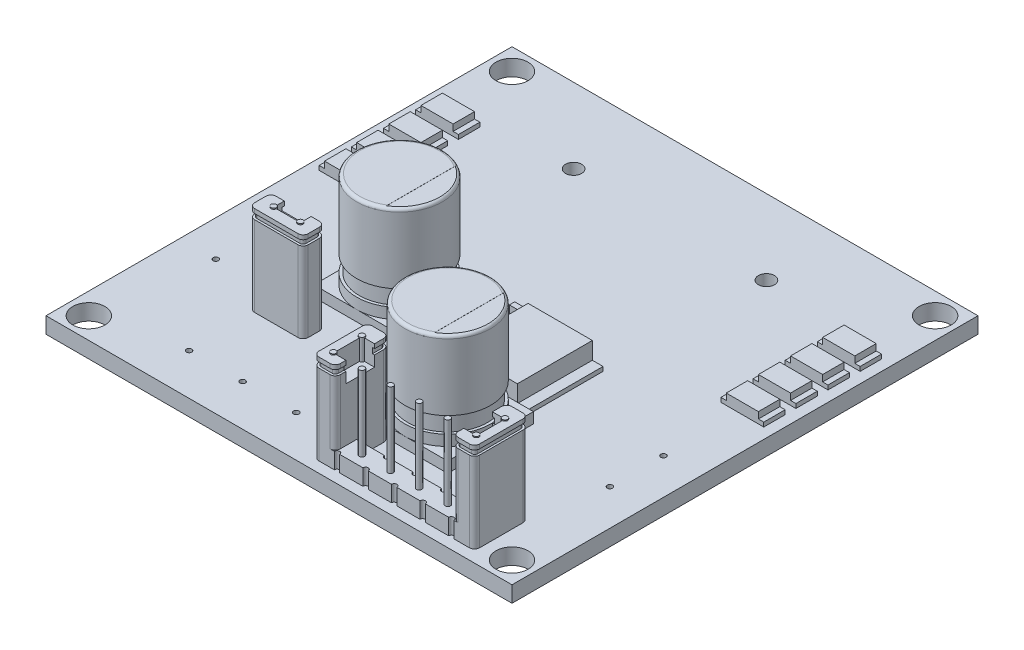
SolidWorks part; units mm, degrees
ref_plane "Ön Düzlem" through (0, 0, 0) normal (0, 0, 1) x (1, 0, 0)
ref_plane "Üst Düzlem" through (0, 0, 0) normal (0, 1, 0) x (1, 0, 0)
ref_plane "Sağ Düzlem" through (0, 0, 0) normal (1, 0, 0) x (0, 0, -1)
sketch "Çizim1" plane through (0, 0, 0) normal (0, 1, 0) x (1, 0, 0)
  line L0 (0, 0) -> (0, 21.75) construction
  line L1 (-21.75, 21.75) -> (21.75, 21.75)
  line L2 (-21.75, 21.75) -> (-21.75, -21.75)
  line L3 (-21.75, -21.75) -> (21.75, -21.75)
  line L4 (21.75, 21.75) -> (21.75, -21.75)
  line L5 (-21.75, 21.75) -> (21.75, -21.75) construction
  line L6 (-21.75, -21.75) -> (21.75, 21.75) construction
  line L7 (0, 21.75) -> (0, 0) construction
  line L8 (0, 0) -> (21.75, 0) construction
  circle A0 centre (-19.75, 19.75) radius 1.5
  circle A1 centre (19.75, 19.75) radius 1.5
  circle A2 centre (19.75, -19.75) radius 1.5
  circle A3 centre (-19.75, -19.75) radius 1.5
  point P0 (0, 0)
  dimension "D3" = 3
  dimension "D5" = 2
  dimension "D1" = 43.5
  dimension "D2" = 43.5
  dimension "D4" = 2
extrude "Yükseklik-Ekstrüzyon1" add sketch "Çizim1" along normal blind 1.5
sketch "Çizim2" plane through (0, 1.5, 0) normal (0, 1, 0) x (1, 0, 0)
  line L0 (0, 21.75) -> (0, 0) construction
  line L1 (21.75, 21.75) -> (-21.75, 21.75) construction
  line L2 (-21.75, 14.75) -> (21.75, 14.75) construction
  line L3 (-21.75, 21.75) -> (-21.75, -21.75) construction
  line L4 (21.75, -21.75) -> (21.75, 21.75) construction
  circle A0 centre (-9, 14.75) radius 0.75
  circle A1 centre (9, 14.75) radius 0.75
  dimension "D2" = 9
  dimension "D3" = 1.5
  dimension "D1" = 9
  dimension "D4" = 7
extrude "Kes-Ekstrüzyon1" cut sketch "Çizim2" against normal blind 10
sketch "Çizim3" plane through (0, 1.5, 0) normal (0, 1, 0) x (1, 0, 0)
  line L0 (-21.75, -3.75) -> (21.75, -3.75) construction
  line L1 (-21.75, 21.75) -> (-21.75, -21.75) construction
  line L2 (21.75, -21.75) -> (21.75, 21.75) construction
  line L3 (-21.75, -21.75) -> (21.75, -21.75) construction
  line L4 (-6.75, 21.75) -> (-6.75, -21.75) construction
  line L5 (21.75, 21.75) -> (-21.75, 21.75) construction
  line L6 (5.75, 21.75) -> (5.75, -21.75) construction
  line L7 (-10.75, 0.25) -> (-2.75, 0.25)
  line L8 (-10.75, 0.25) -> (-10.75, -7.75)
  line L9 (-10.75, -7.75) -> (-2.75, -7.75)
  line L10 (-2.75, 0.25) -> (-2.75, -7.75)
  line L11 (-10.75, 0.25) -> (-2.75, -7.75) construction
  line L12 (-10.75, -7.75) -> (-2.75, 0.25) construction
  line L13 (-21.75, -11.75) -> (21.75, -11.75) construction
  line L15 (1.75, -7.75) -> (9.75, -7.75)
  line L16 (1.75, -7.75) -> (1.75, -15.75)
  line L17 (1.75, -15.75) -> (9.75, -15.75)
  line L18 (9.75, -7.75) -> (9.75, -15.75)
  line L19 (1.75, -7.75) -> (9.75, -15.75) construction
  line L20 (1.75, -15.75) -> (9.75, -7.75) construction
  point P12 (-6.75, -3.75)
  point P21 (5.75, -11.75)
  dimension "D1" = 18
  dimension "D2" = 15
  dimension "D3" = 8
  dimension "D4" = 8
  dimension "D5" = 16
  dimension "D6" = 10
  dimension "D7" = 8
  dimension "D8" = 8
extrude "Yükseklik-Ekstrüzyon2" add sketch "Çizim3" along normal blind 1
sketch "Çizim4" plane through (0, 2.5, 0) normal (0, 1, 0) x (1, 0, 0)
  line L0 (-10.75, 0.25) -> (-2.75, -7.75) construction
  line L1 (1.75, -7.75) -> (9.75, -15.75) construction
  circle A0 centre (-6.75, -3.75) radius 4
  circle A1 centre (5.75, -11.75) radius 4
extrude "Yükseklik-Ekstrüzyon3" add sketch "Çizim4" along normal blind 1
sketch "Çizim5" plane through (0, 3.5, 0) normal (0, 1, 0) x (1, 0, 0)
  circle A0 centre (-6.75, -3.75) radius 3.75
  circle A1 centre (5.75, -11.75) radius 3.75
  dimension "D1" = 7.5
  dimension "D2" = 7.5
extrude "Yükseklik-Ekstrüzyon4" add sketch "Çizim5" along normal blind 1.5
sketch "Çizim6" plane through (0, 5, 0) normal (0, 1, 0) x (1, 0, 0)
  circle A0 centre (-6.75, -3.75) radius 4
  circle A1 centre (5.75, -11.75) radius 4
extrude "Yükseklik-Ekstrüzyon5" add sketch "Çizim6" along normal blind 6.5
fillet "Radyus1" radius 0.3 2 edges at (5.75, 11.5, 15.75) (-6.75, 11.5, 7.75)
sketch "Çizim7" plane through (0, 11.5, 0) normal (0, 1, 0) x (1, 0, 0)
  line L0 (-6.75, -3.75) -> (-6.75, 0.25) construction
  line L1 (-4.7498, -0.286) -> (-4.7498, -7.214)
  line L2 (5.75, -11.75) -> (5.75, -7.75) construction
  line L3 (7.75, -8.2859) -> (7.75, -15.2141)
  arc A0 (-4.7498, -7.214) -> (-4.7498, -0.286) centre (-6.75, -3.75) ccw
  arc A1 (7.75, -15.2141) -> (7.75, -8.2859) centre (5.75, -11.75) ccw
  dimension "D1" = 2.0002
  dimension "D2" = 2
extrude "Kes-Ekstrüzyon2" cut sketch "Çizim7" against normal blind 0.01
sketch "Çizim8" plane through (0, 1.5, 0) normal (0, 1, 0) x (1, 0, 0)
  line L0 (21.75, -20.75) -> (15.3333, -20.75) construction
  line L1 (21.75, -21.75) -> (21.75, 21.75) construction
  line L2 (-21.75, 21.75) -> (-21.75, -21.75) construction
  line L3 (-21.75, -21.75) -> (21.75, -21.75) construction
  line L4 (17.25, -21.75) -> (17.25, 21.75) construction
  line L5 (21.75, 21.75) -> (-21.75, 21.75) construction
  line L6 (4.25, -18.75) -> (6.8333, -18.75)
  line L7 (16.7735, -20.75) -> (15.3333, -20.75)
  line L8 (17.25, -20.2735) -> (17.25, -16.2265)
  line L9 (16.7735, -15.75) -> (15.7265, -15.75)
  line L10 (2.25, -20.2735) -> (2.25, -16.2265)
  line L11 (4.25, -16.2265) -> (4.25, -18.75)
  line L12 (15.25, -16.2265) -> (15.25, -18.75)
  line L13 (3.7735, -15.75) -> (2.7265, -15.75)
  line L15 (6.8333, -20.75) -> (4.6667, -20.75)
  line L16 (6.8333, -20.75) -> (4.6667, -20.75) construction
  line L17 (2.25, -19.75) -> (17.25, -19.75) construction
  line L18 (16.425, -19.75) -> (16.425, -15.75) construction
  line L19 (10, -18.75) -> (12.1667, -18.75)
  line L20 (9.5, -20.75) -> (7.3333, -20.75)
  line L21 (9.5, -20.75) -> (7.3333, -20.75) construction
  line L22 (12.6667, -18.75) -> (15.25, -18.75)
  line L23 (12.1667, -20.75) -> (10, -20.75) construction
  line L24 (12.1667, -20.75) -> (10, -20.75)
  line L25 (14.8333, -20.75) -> (12.6667, -20.75) construction
  line L26 (14.8333, -20.75) -> (12.6667, -20.75)
  line L27 (4.1667, -20.75) -> (2.7265, -20.75)
  line L28 (4.1667, -20.75) -> (-21.75, -20.75) construction
  line L29 (7.3333, -18.75) -> (9.5, -18.75)
  circle A0 centre (19.75, -19.75) radius 1.5 construction
  arc A1 (15.25, -16.2265) -> (15.7265, -15.75) centre (15.7265, -16.2265) cw
  arc A2 (17.25, -16.2265) -> (16.7735, -15.75) centre (16.7735, -16.2265) ccw
  arc A3 (16.7735, -20.75) -> (17.25, -20.2735) centre (16.7735, -20.2735) ccw
  arc A4 (2.7265, -20.75) -> (2.25, -20.2735) centre (2.7265, -20.2735) cw
  arc A5 (4.25, -16.2265) -> (3.7735, -15.75) centre (3.7735, -16.2265) ccw
  arc A6 (2.7265, -15.75) -> (2.25, -16.2265) centre (2.7265, -16.2265) ccw
  circle A7 centre (11.085, -19.75) radius 0.25
  circle A8 centre (13.755, -19.75) radius 0.25
  circle A9 centre (16.425, -19.75) radius 0.25
  circle A10 centre (16.425, -17.08) radius 0.25
  arc A11 (9.5, -18.75) -> (10, -18.75) centre (9.75, -18.75) ccw
  arc A12 (12.1667, -18.75) -> (12.6667, -18.75) centre (12.4167, -18.75) ccw
  arc A13 (10, -20.75) -> (9.5, -20.75) centre (9.75, -20.75) ccw
  arc A14 (12.6667, -20.75) -> (12.1667, -20.75) centre (12.4167, -20.75) ccw
  arc A15 (15.3333, -20.75) -> (14.8333, -20.75) centre (15.0833, -20.75) ccw
  circle A16 centre (3.075, -17.08) radius 0.25
  circle A17 centre (3.075, -19.75) radius 0.25
  arc A18 (4.1667, -20.75) -> (4.6667, -20.75) centre (4.4167, -20.75) cw
  circle A19 centre (5.745, -19.75) radius 0.25
  arc A20 (6.8333, -20.75) -> (7.3333, -20.75) centre (7.0833, -20.75) cw
  arc A21 (7.3333, -18.75) -> (6.8333, -18.75) centre (7.0833, -18.75) cw
  circle A22 centre (8.415, -19.75) radius 0.25
  point P26 (17.25, -15.75)
  point P29 (17.25, -20.75)
  point P32 (2.25, -20.75)
  point P35 (4.25, -15.75)
  dimension "D2" = 2.5
  dimension "D8" = 0.4765
  dimension "D13" = 0.5
  dimension "D14" = 2.67
  dimension "D15" = 2.67
  dimension "D16" = 2.67
  dimension "D17" = 0.5
  dimension "D18" = 0.5
  dimension "D1" = 1
  dimension "D3" = 5
  dimension "D4" = 2
  dimension "D5" = 15
  dimension "D6" = 2
  dimension "D7" = 2
  dimension "D11" = 1
extrude "Yükseklik-Ekstrüzyon6" add sketch "Çizim8" along normal blind 1.5
sketch "Çizim9" plane through (0, 3, 0) normal (0, 1, 0) x (1, 0, 0)
  circle A0 centre (3.075, -17.08) radius 0.25
  circle A1 centre (3.075, -19.75) radius 0.25
  circle A2 centre (5.745, -19.75) radius 0.25
  circle A3 centre (8.415, -19.75) radius 0.25
  circle A4 centre (11.085, -19.75) radius 0.25
  circle A5 centre (13.755, -19.75) radius 0.25
  circle A6 centre (16.425, -19.75) radius 0.25
  circle A7 centre (16.425, -17.08) radius 0.25
extrude "Kes-Ekstrüzyon3" cut sketch "Çizim9" against normal blind 5
sketch "Çizim10" plane through (0, 3, 0) normal (0, 1, 0) x (1, 0, 0)
  circle A0 centre (3.075, -17.08) radius 0.25
  circle A1 centre (3.075, -19.75) radius 0.25
  circle A2 centre (5.745, -19.75) radius 0.25
  circle A3 centre (8.415, -19.75) radius 0.25
  circle A4 centre (11.085, -19.75) radius 0.25
  circle A5 centre (13.755, -19.75) radius 0.25
  circle A6 centre (16.425, -19.75) radius 0.25
  circle A7 centre (16.425, -17.08) radius 0.25
extrude "Yükseklik-Ekstrüzyon7" add sketch "Çizim10" along normal blind 7 and the other way blind 3.5
sketch "Çizim11" plane through (0, 3, 0) normal (0, 1, 0) x (1, 0, 0)
  line L0 (9.75, -19) -> (9.75, -20.5) construction
  line L1 (3.25, -15.75) -> (3.25, -20.75) construction
  line L2 (3.7735, -15.75) -> (2.7265, -15.75) construction
  line L3 (2.7265, -20.75) -> (4.1667, -20.75) construction
  line L4 (16.7735, -20.75) -> (15.7265, -20.75)
  line L5 (2.7265, -15.75) -> (3.7735, -15.75)
  line L6 (2.25, -16.2265) -> (2.25, -20.2735)
  line L7 (2.7265, -20.75) -> (3.7735, -20.75)
  line L8 (4.25, -16.2265) -> (4.25, -20.2735)
  line L9 (2.25, -15.75) -> (4.25, -20.75) construction
  line L10 (2.25, -20.75) -> (4.25, -15.75) construction
  line L11 (15.25, -16.2265) -> (15.25, -20.2735)
  line L12 (16.7735, -15.75) -> (15.7265, -15.75)
  line L13 (17.25, -16.2265) -> (17.25, -20.2735)
  arc A0 (9.5, -18.75) -> (10, -18.75) centre (9.75, -18.75) ccw construction
  arc A1 (10, -20.75) -> (9.5, -20.75) centre (9.75, -20.75) ccw construction
  arc A2 (3.7735, -20.75) -> (4.25, -20.2735) centre (3.7735, -20.2735) ccw
  arc A3 (2.25, -20.2735) -> (2.7265, -20.75) centre (2.7265, -20.2735) ccw
  arc A4 (3.7735, -15.75) -> (4.25, -16.2265) centre (3.7735, -16.2265) cw
  arc A5 (2.7265, -15.75) -> (2.25, -16.2265) centre (2.7265, -16.2265) ccw
  circle A6 centre (3.075, -17.08) radius 0.25
  circle A7 centre (3.075, -19.75) radius 0.25
  circle A8 centre (16.425, -19.75) radius 0.25
  circle A9 centre (16.425, -17.08) radius 0.25
  arc A10 (15.7265, -20.75) -> (15.25, -20.2735) centre (15.7265, -20.2735) cw
  arc A11 (15.7265, -15.75) -> (15.25, -16.2265) centre (15.7265, -16.2265) ccw
  arc A12 (17.25, -20.2735) -> (16.7735, -20.75) centre (16.7735, -20.2735) cw
  arc A13 (16.7735, -15.75) -> (17.25, -16.2265) centre (16.7735, -16.2265) cw
  point P14 (3.25, -18.25)
  dimension "D1" = 0.4765
extrude "Yükseklik-Ekstrüzyon8" add sketch "Çizim11" along normal blind 5
sketch "Çizim12" plane through (0, 8, 0) normal (0, 1, 0) x (1, 0, 0)
  line L0 (3.25, -16.8151) -> (3.25, -19.6849) construction
  line L3 (3.325, -17.08) -> (4.25, -17.08)
  line L4 (2.7265, -15.75) -> (3.7735, -15.75)
  line L5 (2.25, -16.2265) -> (2.25, -20.2735)
  line L6 (2.7265, -20.75) -> (3.7735, -20.75)
  line L7 (4.25, -16.2265) -> (4.25, -17.08)
  line L8 (2.25, -15.75) -> (4.25, -20.75) construction
  line L9 (2.25, -20.75) -> (4.25, -15.75) construction
  line L10 (3.325, -19.75) -> (4.25, -19.75)
  line L11 (4.25, -19.75) -> (4.25, -20.2735)
  line L12 (3.075, -17.33) -> (3.075, -19.5)
  line L13 (9.75, -19) -> (9.75, -20.5) construction
  line L14 (16.175, -17.08) -> (15.25, -17.08)
  line L15 (15.25, -16.2265) -> (15.25, -17.08)
  line L16 (16.7735, -15.75) -> (15.7265, -15.75)
  line L17 (17.25, -16.2265) -> (17.25, -20.2735)
  line L18 (16.7735, -20.75) -> (15.7265, -20.75)
  line L19 (15.25, -19.75) -> (15.25, -20.2735)
  line L20 (16.175, -19.75) -> (15.25, -19.75)
  line L21 (16.425, -17.33) -> (16.425, -19.5)
  arc A0 (3.7735, -20.75) -> (4.25, -20.2735) centre (3.7735, -20.2735) ccw
  arc A1 (2.25, -20.2735) -> (2.7265, -20.75) centre (2.7265, -20.2735) ccw
  arc A2 (3.7735, -15.75) -> (4.25, -16.2265) centre (3.7735, -16.2265) cw
  arc A3 (2.7265, -15.75) -> (2.25, -16.2265) centre (2.7265, -16.2265) ccw
  arc A4 (3.325, -17.08) -> (3.075, -17.33) centre (3.075, -17.08) ccw
  arc A5 (3.075, -19.5) -> (3.325, -19.75) centre (3.075, -19.75) ccw
  arc A6 (9.5, -18.75) -> (10, -18.75) centre (9.75, -18.75) ccw construction
  arc A7 (10, -20.75) -> (9.5, -20.75) centre (9.75, -20.75) ccw construction
  arc A8 (16.175, -17.08) -> (16.425, -17.33) centre (16.425, -17.08) cw
  arc A9 (15.7265, -15.75) -> (15.25, -16.2265) centre (15.7265, -16.2265) ccw
  arc A10 (16.7735, -15.75) -> (17.25, -16.2265) centre (16.7735, -16.2265) cw
  arc A11 (17.25, -20.2735) -> (16.7735, -20.75) centre (16.7735, -20.2735) cw
  arc A12 (15.7265, -20.75) -> (15.25, -20.2735) centre (15.7265, -20.2735) cw
  arc A13 (16.425, -19.5) -> (16.175, -19.75) centre (16.425, -19.75) cw
  point P6 (3.25, -18.25)
  dimension "D1" = 0.4765
extrude "Yükseklik-Ekstrüzyon10" add sketch "Çizim12" along normal blind 1
sketch "Çizim13" plane through (0, 9, 0) normal (0, 1, 0) x (1, 0, 0)
  line L0 (3.25, -15.75) -> (3.25, -15.757) construction
  line L1 (2.7265, -15.75) -> (3.7735, -15.75) construction
  line L2 (2.7265, -20.75) -> (4.1667, -20.75) construction
  line L3 (3.075, -17.33) -> (3.075, -19.5)
  line L8 (2.2382, -15.757) -> (2.322, -15.9636) construction
  line L9 (2.2382, -20.743) -> (2.322, -20.5364) construction
  line L10 (3.325, -17.08) -> (4.0618, -17.08)
  line L11 (3.325, -19.75) -> (4.0618, -19.75)
  line L12 (2.4382, -16.2335) -> (2.4382, -20.2665)
  line L13 (2.7147, -20.543) -> (3.7853, -20.543)
  line L14 (4.0618, -16.2335) -> (4.0618, -17.08)
  line L15 (2.7147, -15.957) -> (3.7853, -15.957)
  line L16 (2.4382, -16.2498) -> (4.178, -20.5364) construction
  line L17 (4.0618, -19.75) -> (4.0618, -20.2665)
  line L18 (3.25, -15.957) -> (3.25, -20.75) construction
  line L19 (4.178, -15.9636) -> (4.2618, -15.757) construction
  line L20 (9.75, -19) -> (9.75, -20.5) construction
  line L21 (16.7853, -15.957) -> (15.7147, -15.957)
  line L22 (2.4382, -20.2502) -> (4.0618, -16.2498) construction
  line L23 (17.0618, -16.2335) -> (17.0618, -20.2665)
  line L24 (16.7853, -20.543) -> (15.7147, -20.543)
  line L25 (15.4382, -19.75) -> (15.4382, -20.2665)
  line L26 (16.175, -19.75) -> (15.4382, -19.75)
  line L27 (16.425, -17.33) -> (16.425, -19.5)
  line L28 (16.175, -17.08) -> (15.4382, -17.08)
  line L29 (15.4382, -16.2335) -> (15.4382, -17.08)
  arc A4 (3.325, -17.08) -> (3.075, -17.33) centre (3.075, -17.08) ccw
  arc A5 (3.075, -19.5) -> (3.325, -19.75) centre (3.075, -19.75) ccw
  arc A6 (2.4382, -20.2665) -> (2.7147, -20.543) centre (2.7147, -20.2665) ccw
  arc A7 (3.7853, -20.543) -> (4.0618, -20.2665) centre (3.7853, -20.2665) ccw
  arc A8 (3.7853, -15.957) -> (4.0618, -16.2335) centre (3.7853, -16.2335) cw
  arc A9 (2.7147, -15.957) -> (2.4382, -16.2335) centre (2.7147, -16.2335) ccw
  arc A10 (9.5, -18.75) -> (10, -18.75) centre (9.75, -18.75) ccw construction
  arc A11 (10, -20.75) -> (9.5, -20.75) centre (9.75, -20.75) ccw construction
  arc A12 (15.7147, -15.957) -> (15.4382, -16.2335) centre (15.7147, -16.2335) ccw
  arc A13 (16.7853, -15.957) -> (17.0618, -16.2335) centre (16.7853, -16.2335) cw
  arc A14 (17.0618, -20.2665) -> (16.7853, -20.543) centre (16.7853, -20.2665) cw
  arc A15 (15.7147, -20.543) -> (15.4382, -20.2665) centre (15.7147, -20.2665) cw
  arc A16 (16.425, -19.5) -> (16.175, -19.75) centre (16.425, -19.75) cw
  arc A17 (16.175, -17.08) -> (16.425, -17.33) centre (16.425, -17.08) cw
  point P6 (3.25, -18.25)
extrude "Yükseklik-Ekstrüzyon11" add sketch "Çizim13" along normal blind 0.5
sketch "Çizim14" plane through (0, 9.5, 0) normal (0, 1, 0) x (1, 0, 0)
  line L0 (3.25, -15.957) -> (3.25, -20.543) construction
  line L1 (3.7853, -15.957) -> (2.7147, -15.957) construction
  line L2 (2.7147, -20.543) -> (3.7853, -20.543) construction
  line L3 (4.25, -17.08) -> (3.325, -17.08)
  line L4 (2.7265, -15.75) -> (3.7735, -15.75)
  line L5 (2.25, -16.2265) -> (2.25, -20.2735)
  line L6 (2.7265, -20.75) -> (3.7735, -20.75)
  line L7 (4.25, -16.2265) -> (4.25, -17.08)
  line L8 (2.25, -15.75) -> (4.25, -20.75) construction
  line L9 (2.25, -20.75) -> (4.25, -15.75) construction
  line L10 (3.075, -17.33) -> (3.075, -19.5)
  line L11 (3.325, -19.75) -> (4.25, -19.75)
  line L12 (4.25, -19.75) -> (4.25, -20.2735)
  line L13 (9.75, -19) -> (9.75, -20.5) construction
  line L14 (15.25, -17.08) -> (16.175, -17.08)
  line L15 (15.25, -16.2265) -> (15.25, -17.08)
  line L16 (16.7735, -15.75) -> (15.7265, -15.75)
  line L17 (17.25, -16.2265) -> (17.25, -20.2735)
  line L18 (16.7735, -20.75) -> (15.7265, -20.75)
  line L19 (15.25, -19.75) -> (15.25, -20.2735)
  line L20 (16.175, -19.75) -> (15.25, -19.75)
  line L21 (16.425, -17.33) -> (16.425, -19.5)
  arc A0 (3.7735, -15.75) -> (4.25, -16.2265) centre (3.7735, -16.2265) cw
  arc A1 (2.7265, -15.75) -> (2.25, -16.2265) centre (2.7265, -16.2265) ccw
  arc A2 (3.7735, -20.75) -> (4.25, -20.2735) centre (3.7735, -20.2735) ccw
  arc A3 (2.25, -20.2735) -> (2.7265, -20.75) centre (2.7265, -20.2735) ccw
  arc A4 (3.325, -17.08) -> (3.075, -17.33) centre (3.075, -17.08) ccw
  arc A5 (3.075, -19.5) -> (3.325, -19.75) centre (3.075, -19.75) ccw
  arc A6 (9.5, -18.75) -> (10, -18.75) centre (9.75, -18.75) ccw construction
  arc A7 (10, -20.75) -> (9.5, -20.75) centre (9.75, -20.75) ccw construction
  arc A8 (16.175, -17.08) -> (16.425, -17.33) centre (16.425, -17.08) cw
  arc A9 (15.7265, -15.75) -> (15.25, -16.2265) centre (15.7265, -16.2265) ccw
  arc A10 (16.7735, -15.75) -> (17.25, -16.2265) centre (16.7735, -16.2265) cw
  arc A11 (17.25, -20.2735) -> (16.7735, -20.75) centre (16.7735, -20.2735) cw
  arc A12 (15.7265, -20.75) -> (15.25, -20.2735) centre (15.7265, -20.2735) cw
  arc A13 (16.425, -19.5) -> (16.175, -19.75) centre (16.425, -19.75) cw
  point P6 (3.25, -18.25)
  dimension "D1" = 0.4765
extrude "Yükseklik-Ekstrüzyon12" add sketch "Çizim14" along normal blind 0.4
sketch "Çizim15" plane through (0, 1.5, 0) normal (0, 1, 0) x (1, 0, 0)
  line L0 (-21.75, -17.89) -> (21.75, -17.89) construction
  line L1 (-21.75, 21.75) -> (-21.75, -21.75) construction
  line L2 (21.75, -21.75) -> (21.75, 21.75) construction
  line L3 (-21.75, -21.75) -> (21.75, -21.75) construction
  circle A0 centre (-12.25, -17.89) radius 0.25
  circle A1 centre (-7.25, -17.89) radius 0.25
  circle A2 centre (-2.25, -17.89) radius 0.25
  dimension "D2" = 0.5
  dimension "D3" = 9.5
  dimension "D4" = 5
  dimension "D5" = 5
  dimension "D1" = 3.86
extrude "Kes-Ekstrüzyon4" cut sketch "Çizim15" against normal blind 5
sketch "Çizim16" plane through (0, 1.5, 0) normal (0, 1, 0) x (1, 0, 0)
  line L0 (0, 21.75) -> (0, -21.75) construction
  line L1 (21.75, 21.75) -> (-21.75, 21.75) construction
  line L2 (-21.75, -21.75) -> (21.75, -21.75) construction
  line L3 (18.39, 21.75) -> (18.39, -21.75) construction
  line L4 (21.75, -21.75) -> (21.75, 21.75) construction
  circle A0 centre (18.39, -4.25) radius 0.25
  circle A1 centre (18.39, -9.25) radius 0.25
  circle A2 centre (-18.39, -9.25) radius 0.25
  circle A3 centre (-18.39, -4.25) radius 0.25
  dimension "D3" = 5
  dimension "D4" = 0.5
  dimension "D5" = 0.5
  dimension "D1" = 3.36
  dimension "D2" = 12.5
extrude "Kes-Ekstrüzyon5" cut sketch "Çizim16" against normal blind 7
sketch "Çizim18" plane through (0, 1.5, 0) normal (0, 1, 0) x (1, 0, 0)
  line L0 (18.75, 21.75) -> (18.75, -21.75) construction
  line L1 (21.75, 21.75) -> (-21.75, 21.75) construction
  line L2 (-21.75, -21.75) -> (21.75, -21.75) construction
  line L3 (21.75, -21.75) -> (21.75, 21.75) construction
  line L4 (18.75, 8.25) -> (21.75, 8.25) construction
  line L5 (17.25, 13.75) -> (20.25, 13.75)
  line L6 (17.25, 13.75) -> (17.25, 11.75)
  line L7 (17.25, 11.75) -> (20.25, 11.75)
  line L8 (20.25, 13.75) -> (20.25, 11.75)
  line L9 (17.25, 13.75) -> (20.25, 11.75) construction
  line L10 (17.25, 11.75) -> (20.25, 13.75) construction
  line L11 (17.25, 10.75) -> (20.25, 10.75)
  line L12 (17.25, 10.75) -> (17.25, 8.75)
  line L13 (17.25, 8.75) -> (20.25, 8.75)
  line L14 (20.25, 10.75) -> (20.25, 8.75)
  line L15 (17.25, 10.75) -> (20.25, 8.75) construction
  line L16 (17.25, 8.75) -> (20.25, 10.75) construction
  line L17 (17.25, 7.75) -> (20.25, 7.75)
  line L18 (20.25, 5.75) -> (20.25, 7.75)
  line L19 (17.25, 5.75) -> (20.25, 5.75)
  line L20 (17.25, 5.75) -> (17.25, 7.75)
  line L21 (17.25, 4.75) -> (20.25, 4.75)
  line L22 (20.25, 2.75) -> (20.25, 4.75)
  line L23 (17.25, 2.75) -> (20.25, 2.75)
  line L24 (17.25, 2.75) -> (17.25, 4.75)
  line L25 (0, 21.75) -> (0, 0) construction
  line L26 (-17.25, 2.75) -> (-17.25, 4.75)
  line L27 (-17.25, 2.75) -> (-20.25, 2.75)
  line L28 (-20.25, 2.75) -> (-20.25, 4.75)
  line L29 (-17.25, 4.75) -> (-20.25, 4.75)
  line L30 (-17.25, 5.75) -> (-17.25, 7.75)
  line L31 (-17.25, 5.75) -> (-20.25, 5.75)
  line L32 (-20.25, 5.75) -> (-20.25, 7.75)
  line L33 (-17.25, 7.75) -> (-20.25, 7.75)
  line L34 (-17.25, 8.75) -> (-20.25, 8.75)
  line L35 (-20.25, 10.75) -> (-20.25, 8.75)
  line L36 (-17.25, 10.75) -> (-20.25, 10.75)
  line L37 (-17.25, 10.75) -> (-17.25, 8.75)
  line L38 (-17.25, 11.75) -> (-20.25, 11.75)
  line L39 (-20.25, 13.75) -> (-20.25, 11.75)
  line L40 (-17.25, 13.75) -> (-20.25, 13.75)
  line L41 (-17.25, 13.75) -> (-17.25, 11.75)
  point P8 (18.75, 12.75)
  point P13 (18.75, 9.75)
  dimension "D1" = 3
  dimension "D2" = 2
  dimension "D3" = 3
  dimension "D4" = 8
  dimension "D5" = 2
  dimension "D6" = 1
  dimension "D7" = 0.5
extrude "Yükseklik-Ekstrüzyon13" add sketch "Çizim18" along normal blind 1
sketch "Çizim19" plane through (0, 1.5, 0) normal (0, 1, 0) x (1, 0, 0)
  line L0 (0, 21.75) -> (0, 0) construction
  line L1 (21.75, 21.75) -> (-21.75, 21.75) construction
  line L2 (18.75, 11.75) -> (18.75, 10.75) construction
  line L3 (17.25, 13.75) -> (16.75, 13.75)
  line L4 (17.25, 13.75) -> (17.25, 11.75)
  line L5 (17.25, 11.75) -> (16.75, 11.75)
  line L6 (16.75, 13.75) -> (16.75, 11.75)
  line L7 (20.25, 13.75) -> (20.75, 13.75)
  line L8 (20.25, 13.75) -> (20.25, 11.75)
  line L9 (20.25, 11.75) -> (20.75, 11.75)
  line L10 (20.75, 13.75) -> (20.75, 11.75)
  line L11 (17.25, 11.75) -> (20.25, 11.75) construction
  line L12 (20.25, 10.75) -> (17.25, 10.75) construction
  line L13 (18.75, 10.75) -> (18.75, 11.25) construction
  line L14 (18.75, 11.25) -> (19.385, 11.25) construction
  line L15 (20.25, 10.75) -> (20.75, 10.75)
  line L16 (20.75, 8.75) -> (20.75, 10.75)
  line L17 (20.25, 8.75) -> (20.75, 8.75)
  line L18 (20.25, 8.75) -> (20.25, 10.75)
  line L19 (17.25, 10.75) -> (16.75, 10.75)
  line L20 (16.75, 8.75) -> (16.75, 10.75)
  line L21 (17.25, 8.75) -> (16.75, 8.75)
  line L22 (17.25, 8.75) -> (17.25, 10.75)
  line L23 (18.75, 8.75) -> (18.75, 7.75) construction
  line L24 (17.25, 8.75) -> (20.25, 8.75) construction
  line L25 (20.25, 7.75) -> (17.25, 7.75) construction
  line L26 (18.75, 7.75) -> (18.75, 8.25) construction
  line L27 (18.75, 8.25) -> (19.7606, 8.25) construction
  line L28 (20.25, 7.75) -> (20.25, 5.75)
  line L29 (20.25, 7.75) -> (20.75, 7.75)
  line L30 (20.75, 7.75) -> (20.75, 5.75)
  line L31 (20.25, 5.75) -> (20.75, 5.75)
  line L32 (17.25, 7.75) -> (17.25, 5.75)
  line L33 (17.25, 7.75) -> (16.75, 7.75)
  line L34 (16.75, 7.75) -> (16.75, 5.75)
  line L35 (17.25, 5.75) -> (16.75, 5.75)
  line L36 (20.25, 4.75) -> (20.75, 4.75)
  line L37 (20.75, 2.75) -> (20.75, 4.75)
  line L38 (20.25, 2.75) -> (20.75, 2.75)
  line L39 (20.25, 2.75) -> (20.25, 4.75)
  line L40 (17.25, 4.75) -> (16.75, 4.75)
  line L41 (16.75, 2.75) -> (16.75, 4.75)
  line L42 (17.25, 2.75) -> (16.75, 2.75)
  line L43 (17.25, 2.75) -> (17.25, 4.75)
  line L44 (-20.25, 2.75) -> (-20.25, 4.75)
  line L45 (-20.25, 2.75) -> (-20.75, 2.75)
  line L46 (-20.75, 2.75) -> (-20.75, 4.75)
  line L47 (-20.25, 4.75) -> (-20.75, 4.75)
  line L48 (-17.25, 2.75) -> (-17.25, 4.75)
  line L49 (-17.25, 2.75) -> (-16.75, 2.75)
  line L50 (-16.75, 2.75) -> (-16.75, 4.75)
  line L51 (-17.25, 4.75) -> (-16.75, 4.75)
  line L52 (-20.25, 7.75) -> (-20.75, 7.75)
  line L53 (-20.75, 7.75) -> (-20.75, 5.75)
  line L54 (-20.25, 5.75) -> (-20.75, 5.75)
  line L55 (-20.25, 7.75) -> (-20.25, 5.75)
  line L56 (-17.25, 7.75) -> (-16.75, 7.75)
  line L57 (-16.75, 7.75) -> (-16.75, 5.75)
  line L58 (-17.25, 5.75) -> (-16.75, 5.75)
  line L59 (-17.25, 7.75) -> (-17.25, 5.75)
  line L60 (-17.25, 8.75) -> (-17.25, 10.75)
  line L61 (-17.25, 8.75) -> (-16.75, 8.75)
  line L62 (-16.75, 8.75) -> (-16.75, 10.75)
  line L63 (-17.25, 10.75) -> (-16.75, 10.75)
  line L64 (-20.25, 8.75) -> (-20.25, 10.75)
  line L65 (-20.25, 8.75) -> (-20.75, 8.75)
  line L66 (-20.75, 8.75) -> (-20.75, 10.75)
  line L67 (-20.25, 10.75) -> (-20.75, 10.75)
  line L68 (-20.25, 11.75) -> (-20.75, 11.75)
  line L69 (-20.75, 13.75) -> (-20.75, 11.75)
  line L70 (-20.25, 13.75) -> (-20.75, 13.75)
  line L71 (-20.25, 13.75) -> (-20.25, 11.75)
  line L72 (-17.25, 11.75) -> (-16.75, 11.75)
  line L73 (-16.75, 13.75) -> (-16.75, 11.75)
  line L74 (-17.25, 13.75) -> (-16.75, 13.75)
  line L75 (-17.25, 13.75) -> (-17.25, 11.75)
  dimension "D1" = 0.5
  dimension "D2" = 0.5
extrude "Yükseklik-Ekstrüzyon14" add sketch "Çizim19" along normal blind 0.4
sketch "Çizim20" plane through (0, 1.5, 0) normal (0, 1, 0) x (1, 0, 0)
  line L0 (21.75, -7.25) -> (-2.75, -7.25) construction
  line L1 (21.75, -21.75) -> (21.75, 21.75) construction
  line L2 (-2.75, -7.75) -> (-2.75, 0.25) construction
  line L3 (9.75, -7.75) -> (5.75, -7.75) construction
  line L4 (1.75, -7.75) -> (1.75, 21.75) construction
  line L5 (21.75, 21.75) -> (-21.75, 21.75) construction
  line L7 (1.75, -7.25) -> (7.75, -7.25)
  line L8 (1.75, -7.25) -> (1.75, -0.25)
  line L9 (1.75, -0.25) -> (7.75, -0.25)
  line L10 (7.75, -7.25) -> (7.75, -0.25)
  dimension "D1" = 0.5
  dimension "D2" = 7
  dimension "D3" = 6
extrude "Yükseklik-Ekstrüzyon15" add sketch "Çizim20" along normal blind 2
sketch "Çizim21" plane through (0, 1.5, 0) normal (0, 1, 0) x (1, 0, 0)
  line L1 (7.75, -0.25) -> (8.75, -0.25)
  line L2 (7.75, -0.25) -> (7.75, -7.25)
  line L3 (7.75, -7.25) -> (8.75, -7.25)
  line L4 (8.75, -0.25) -> (8.75, -7.25)
  dimension "D1" = 1
extrude "Yükseklik-Ekstrüzyon16" add sketch "Çizim21" along normal blind 0.4
sketch "Çizim22" plane through (0, 1.5, 0) normal (0, 1, 0) x (1, 0, 0)
  line L0 (1.75, -3.75) -> (-0.8924, -3.75) construction
  line L1 (1.75, -0.25) -> (1.75, -7.25) construction
  line L2 (1.75, -3.25) -> (1.75, -4.25)
  line L3 (0.5, -3.25) -> (1.75, -3.25)
  line L4 (0.5, -3.25) -> (0.5, -4.25)
  line L5 (0.5, -4.25) -> (1.75, -4.25)
  line L7 (0.5, -3.25) -> (1.75, -3.75) construction
  line L8 (0.5, -4.25) -> (1.75, -3.75) construction
  line L9 (1.75, -6.75) -> (0.5, -6.75)
  line L10 (1.75, -0.25) -> (0.5, -0.25)
  line L11 (1.75, -0.25) -> (1.75, -0.75)
  line L12 (1.75, -0.75) -> (0.5, -0.75)
  line L13 (0.5, -0.25) -> (0.5, -0.75)
  line L14 (0.5, -7.25) -> (0.5, -6.75)
  line L15 (1.75, -7.25) -> (0.5, -7.25)
  line L16 (1.75, -7.25) -> (1.75, -6.75)
  dimension "D1" = 0.5
extrude "Yükseklik-Ekstrüzyon17" add sketch "Çizim22" along normal blind 1.5
sketch "Çizim23" plane through (0, 1.5, 0) normal (0, 1, 0) x (1, 0, 0)
  line L0 (-12.75, -21.75) -> (-12.75, 6.8422) construction
  line L1 (-21.75, -21.75) -> (21.75, -21.75) construction
  line L2 (-21.75, 21.75) -> (-21.75, -21.75) construction
  line L3 (-21.75, -11.75) -> (21.75, -11.75) construction
  line L4 (21.75, -21.75) -> (21.75, 21.75) construction
  line L5 (-12.75, -10.75) -> (-7.75, -10.75) construction
  line L6 (-12.2735, -11.75) -> (-8.2265, -11.75)
  line L7 (-12.75, -11.2735) -> (-12.75, -10.2265)
  line L8 (-12.2735, -9.75) -> (-8.2265, -9.75)
  line L9 (-7.75, -11.2735) -> (-7.75, -10.2265)
  arc A0 (-8.2265, -11.75) -> (-7.75, -11.2735) centre (-8.2265, -11.2735) ccw
  arc A1 (-8.2265, -9.75) -> (-7.75, -10.2265) centre (-8.2265, -10.2265) cw
  arc A2 (-12.2735, -11.75) -> (-12.75, -11.2735) centre (-12.2735, -11.2735) cw
  arc A3 (-12.75, -10.2265) -> (-12.2735, -9.75) centre (-12.2735, -10.2265) cw
  circle A4 centre (-11.5, -10.75) radius 0.25
  circle A5 centre (-9, -10.75) radius 0.25
  point P16 (-7.75, -11.75)
  point P21 (-12.75, -11.75)
  point P24 (-12.75, -9.75)
  dimension "D5" = 0.4765
  dimension "D6" = 0.5
  dimension "D7" = 0.5
  dimension "D8" = 2.5
  dimension "D9" = 1.25
  dimension "D1" = 9
  dimension "D2" = 10
  dimension "D3" = 5
  dimension "D4" = 2
extrude "Yükseklik-Ekstrüzyon18" add sketch "Çizim23" along normal up to surface (7.5 mm away) up to face at (3.4312, 9, 18.283)
sketch "Çizim24" plane through (0, 1.5, 0) normal (0, 1, 0) x (1, 0, 0)
  circle A0 centre (-11.5, -10.75) radius 0.25
  circle A1 centre (-9, -10.75) radius 0.25
extrude "Yükseklik-Ekstrüzyon19" add sketch "Çizim24" along normal up to surface and the other way up to surface up to face at (11.085, 10, 20) other way up to face at (3.075, -0.5, 17.33)
sketch "Çizim25" plane through (0, 9, 0) normal (0, 1, 0) x (1, 0, 0)
  line L0 (-12.75, -10.75) -> (-11.5, -10.75) construction
  line L1 (-12.75, -10.2265) -> (-12.75, -11.2735) construction
  line L2 (-7.75, -11.2735) -> (-7.75, -10.2265) construction
  line L3 (-12.55, -10.2265) -> (-12.55, -11.2735)
  line L8 (-12.75, -9.75) -> (-7.75, -11.75) construction
  line L9 (-12.75, -11.75) -> (-7.75, -9.75) construction
  line L10 (-12.2735, -11.55) -> (-8.2265, -11.55)
  line L11 (-7.95, -10.2265) -> (-7.95, -11.2735)
  line L12 (-12.2735, -9.95) -> (-11.5, -9.95)
  line L13 (-11.5, -10.5) -> (-11.5, -9.95)
  line L14 (-9, -10.5) -> (-9, -9.95)
  line L15 (-9, -9.95) -> (-8.2265, -9.95)
  line L16 (-9, -10.75) -> (-7.75, -10.75) construction
  line L17 (-11.25, -10.75) -> (-9.25, -10.75)
  line L18 (-11.25, -10.75) -> (-9.25, -10.75) construction
  arc A4 (-12.55, -11.2735) -> (-12.2735, -11.55) centre (-12.2735, -11.2735) ccw
  arc A5 (-8.2265, -11.55) -> (-7.95, -11.2735) centre (-8.2265, -11.2735) ccw
  arc A6 (-8.2265, -9.95) -> (-7.95, -10.2265) centre (-8.2265, -10.2265) cw
  arc A7 (-12.2735, -9.95) -> (-12.55, -10.2265) centre (-12.2735, -10.2265) ccw
  arc A8 (-11.5, -10.5) -> (-11.25, -10.75) centre (-11.5, -10.75) ccw
  arc A9 (-9.25, -10.75) -> (-9, -10.5) centre (-9, -10.75) ccw
  point P6 (-10.25, -10.75)
extrude "Yükseklik-Ekstrüzyon20" add sketch "Çizim25" along normal blind 0.5
sketch "Çizim27" plane through (0, 9.5, 0) normal (0, 1, 0) x (1, 0, 0)
  line L0 (-12.55, -10.75) -> (-11.75, -10.75) construction
  line L1 (-12.55, -10.2265) -> (-12.55, -11.2735) construction
  line L2 (-7.95, -11.2735) -> (-7.95, -10.2265) construction
  line L3 (-11.5, -9.75) -> (-11.5, -10.5)
  line L4 (-12.2735, -9.75) -> (-11.5, -9.75)
  line L5 (-12.75, -10.2265) -> (-12.75, -11.2735)
  line L6 (-12.2735, -11.75) -> (-8.2265, -11.75)
  line L7 (-7.75, -10.2265) -> (-7.75, -11.2735)
  line L8 (-12.75, -9.75) -> (-7.75, -11.75) construction
  line L9 (-12.75, -11.75) -> (-7.75, -9.75) construction
  line L10 (-11.25, -10.75) -> (-9.25, -10.75)
  line L11 (-9, -10.5) -> (-9, -9.75)
  line L12 (-9, -9.75) -> (-8.2265, -9.75)
  line L13 (-11.25, -10.75) -> (-9.25, -10.75) construction
  line L14 (-8.75, -10.75) -> (-7.95, -10.75) construction
  arc A0 (-8.2265, -11.75) -> (-7.75, -11.2735) centre (-8.2265, -11.2735) ccw
  arc A1 (-12.75, -11.2735) -> (-12.2735, -11.75) centre (-12.2735, -11.2735) ccw
  arc A2 (-8.2265, -9.75) -> (-7.75, -10.2265) centre (-8.2265, -10.2265) cw
  arc A3 (-12.2735, -9.75) -> (-12.75, -10.2265) centre (-12.2735, -10.2265) ccw
  arc A4 (-11.5, -10.5) -> (-11.25, -10.75) centre (-11.5, -10.75) ccw
  arc A5 (-9.25, -10.75) -> (-9, -10.5) centre (-9, -10.75) ccw
  point P6 (-10.25, -10.75)
  dimension "D1" = 0.4765
extrude "Yükseklik-Ekstrüzyon21" add sketch "Çizim27" along normal up to surface (0.4 mm away) up to face at (3.3355, 9.9, 18.3207)
